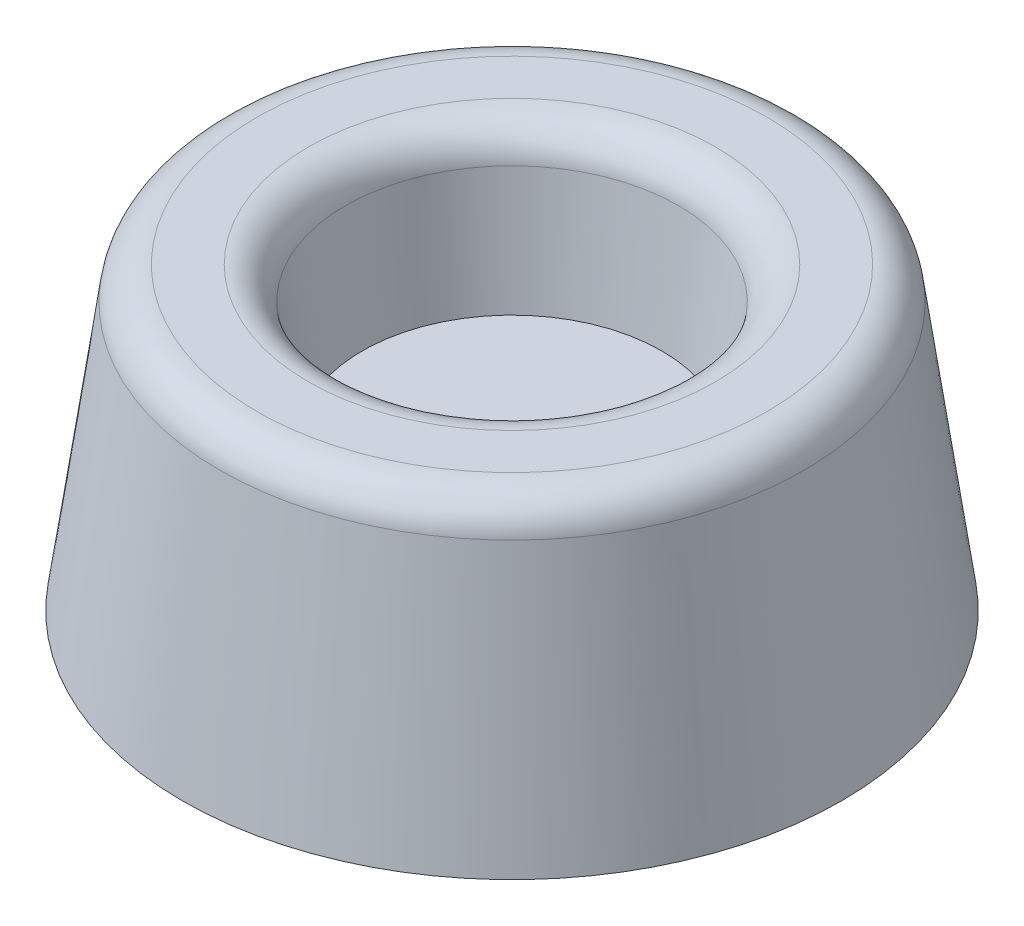
SolidWorks part; units mm, degrees
material "Silicon Rubber"
ref_plane "Front Plane" through (0, 0, 0) normal (0, 0, 1) x (1, 0, 0)
ref_plane "Top Plane" through (0, 0, 0) normal (0, 1, 0) x (1, 0, 0)
ref_plane "Right Plane" through (0, 0, 0) normal (1, 0, 0) x (0, 0, -1)
sketch "Sketch1" plane through (0, 0, 0) normal (1, 0, 0) x (0, 0, -1)
  line L0 (0, 0) -> (0, 14676.5782) construction
  line L1 (0, 0) -> (11.176, 0)
  line L2 (11.176, 0) -> (9.9018, 9.0667)
  line L3 (8.6441, 10.16) -> (6.8979, 10.16)
  line L4 (5.6403, 9.0667) -> (5.08, 5.08)
  line L5 (5.08, 5.08) -> (0, 5.08)
  line L6 (0, 5.08) -> (0, 0)
  arc A0 (9.9018, 9.0667) -> (8.6441, 10.16) centre (8.6441, 8.89) ccw
  arc A1 (6.8979, 10.16) -> (5.6403, 9.0667) centre (6.8979, 8.89) ccw
  dimension "D4" = 1.27
  dimension "D1" = 10.16
  dimension "D2" = 22.352
  dimension "D3" = 5.08
  dimension "D5" = 8
  dimension "D6" = 8
  dimension "D7" = 10.16
revolve "Revolve1" add sketch "Sketch1" angle 360 about L0
